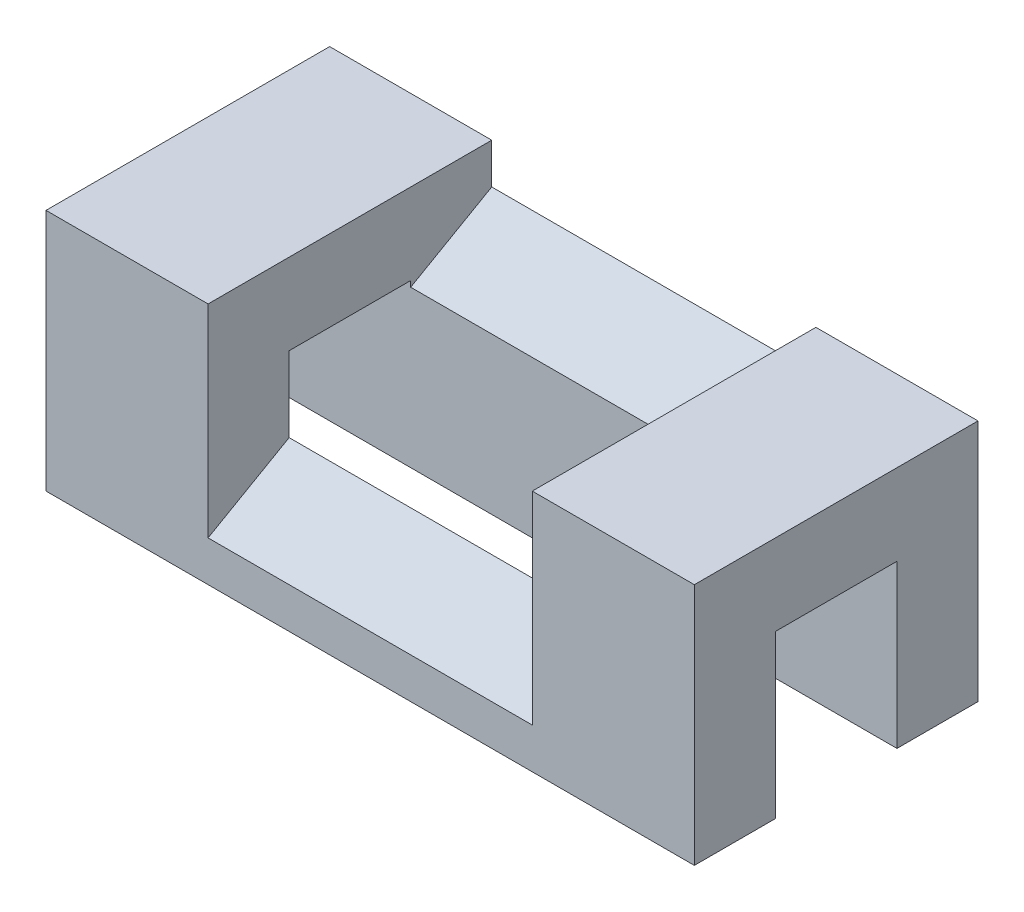
SolidWorks part; units mm, degrees
ref_plane "Front Plane" through (0, 0, 0) normal (0, 0, 1) x (1, 0, 0)
ref_plane "Top Plane" through (0, 0, 0) normal (0, 1, 0) x (1, 0, 0)
ref_plane "Right Plane" through (0, 0, 0) normal (1, 0, 0) x (0, 0, -1)
sketch "Sketch1" plane through (0, 0, 0) normal (1, 0, 0) x (0, 0, -1)
  line L0 (0, 0) -> (0, 30)
  line L1 (0, 30) -> (35, 30)
  line L2 (35, 30) -> (35, 0)
  line L3 (35, 0) -> (25, 0)
  line L4 (10, 0) -> (10, 20)
  line L5 (10, 20) -> (25, 20)
  line L6 (25, 20) -> (25, 0)
  line L8 (10, 0) -> (0, 0)
  dimension "D1" = 30
  dimension "D2" = 35
  dimension "D3" = 20
  dimension "D4" = 10
  dimension "D5" = 10
extrude "Boss-Extrude1" add sketch "Sketch1" against normal blind 80
sketch "Sketch2" plane through (0, 0, 0) normal (1, 0, 0) x (0, 0, -1)
  line L0 (35, 30) -> (35, 25)
  line L1 (35, 0) -> (35, 30) construction
  line L2 (35, 25) -> (0, 5)
  line L4 (0, 5) -> (0, 30)
  line L5 (0, 30) -> (35, 30)
  line L6 (0, 30) -> (0, 0) construction
  point P5 (0, 10.9102)
  dimension "D1" = 5
  dimension "D2" = 5
extrude "Cut-Extrude1" cut sketch "Sketch2" against normal blind 20 and the other way blind 20 from offset 40
